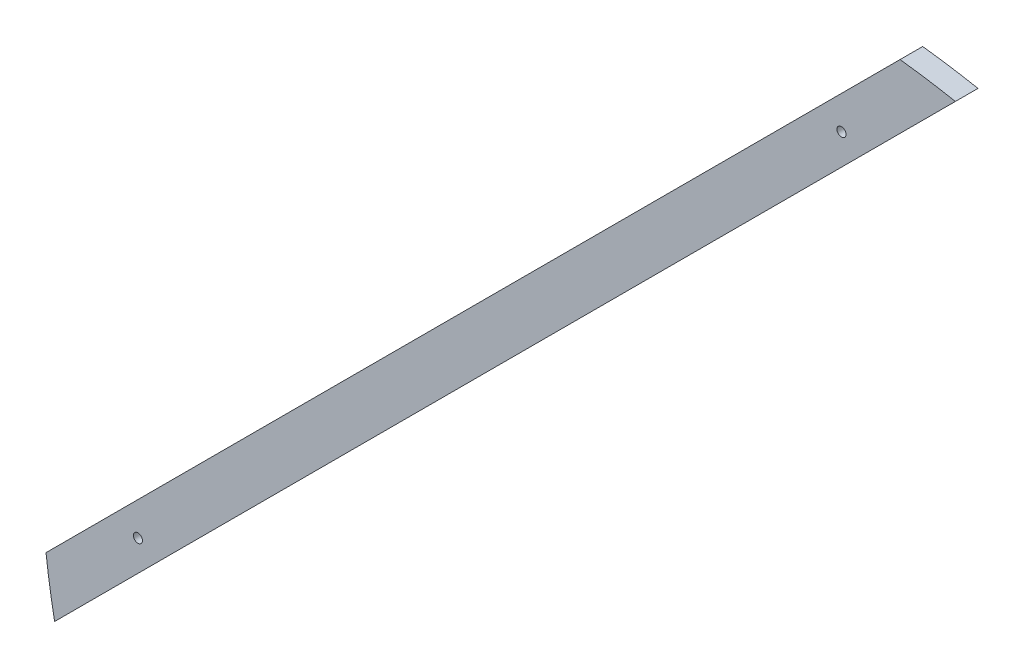
SolidWorks part; units mm, degrees
ref_plane "Plan de face" through (0, 0, 0) normal (0, 0, 1) x (1, 0, 0)
ref_plane "Plan de dessus" through (0, 0, 0) normal (0, 1, 0) x (1, 0, 0)
ref_plane "Plan de droite" through (0, 0, 0) normal (1, 0, 0) x (0, 0, -1)
sketch "Esquisse4" plane through (0, 0, 0) normal (0, 0, 1) x (1, 0, 0)
  line L1 (20.0292, 168.816) -> (15.0794, 163.8662)
  line L2 (15.0794, 163.8662) -> (22.1505, 156.7952) construction
  line L3 (22.1505, 156.7952) -> (32.2653, 166.91)
  line L4 (0, 0) -> (-144.8384, 144.8384) construction
  line L5 (-163.8662, -15.0794) -> (-156.7952, -22.1505) construction
  line L6 (-168.816, -20.0292) -> (-163.8662, -15.0794)
  line L7 (-156.7952, -22.1505) -> (-166.91, -32.2653)
  line L8 (22.1505, 156.7952) -> (-156.7952, -22.1505)
  line L9 (15.0794, 163.8662) -> (-163.8662, -15.0794)
  arc A0 (20.0292, 168.816) -> (32.2653, 166.91) centre (0, 0) cw
  arc A1 (-168.816, -20.0292) -> (-166.91, -32.2653) centre (0, 0) ccw
extrude "Boss.-Extru.1" add sketch "Esquisse4" along normal blind 5
sketch "Esquisse5" plane through (0, 0, 0) normal (0, 0, -1) x (-1, 0, 0)
  line L0 (0, 0) -> (92.266, 92.266) construction
  line L3 (-36.2937, 177.7151) -> (191.4277, -50.0064) construction
  circle A0 centre (148.4924, -7.0711) radius 1
  circle A1 centre (-7.0711, 148.4924) radius 1
  dimension "D2" = 220
  dimension "D1" = 100
  dimension "D3" = 110
extrude "Enlèv. mat.-Extru.1" cut sketch "Esquisse5" against normal through all
